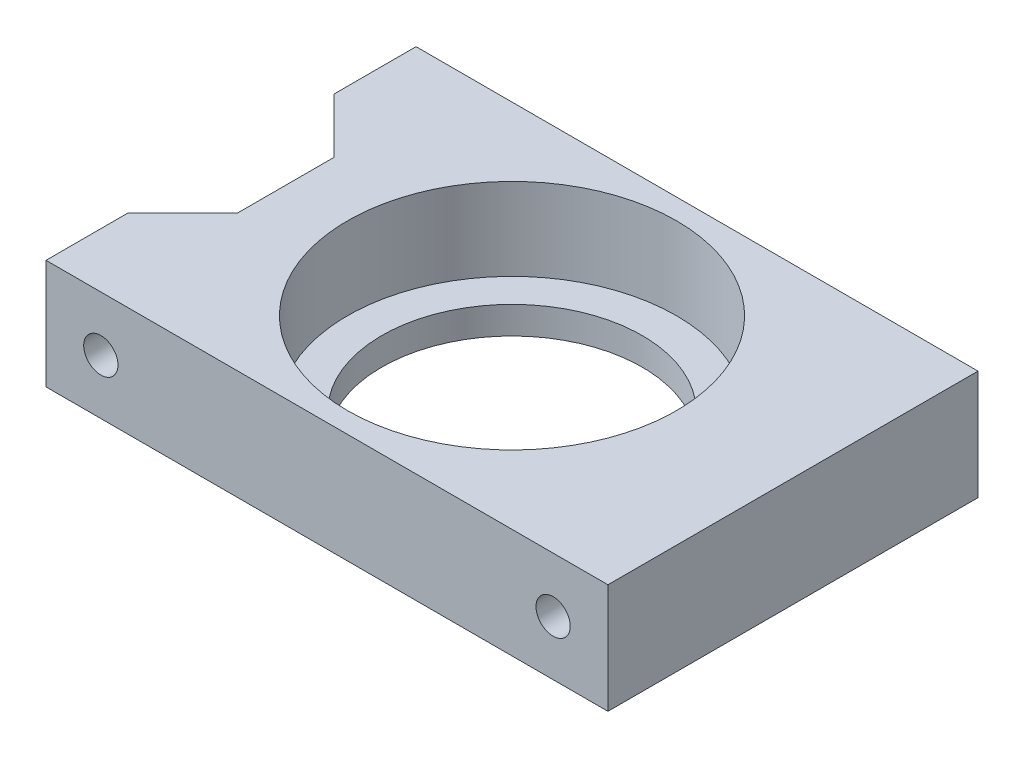
SolidWorks part; units mm, degrees
ref_plane "Спереди" through (0, 0, 0) normal (0, 0, 1) x (1, 0, 0)
ref_plane "Сверху" through (0, 0, 0) normal (0, 1, 0) x (1, 0, 0)
ref_plane "Справа" through (0, 0, 0) normal (1, 0, 0) x (0, 0, -1)
sketch "Эскиз1" plane through (0, 0, 0) normal (0, 1, 0) x (1, 0, 0)
  line L1 (-20.5, -13.5) -> (20.5, -13.5)
  line L2 (-20.5, -13.5) -> (-20.5, 13.5)
  line L3 (-20.5, 13.5) -> (20.5, 13.5)
  line L4 (20.5, -13.5) -> (20.5, 13.5)
  line L5 (-20.5, -13.5) -> (20.5, 13.5) construction
  line L6 (-20.5, 13.5) -> (20.5, -13.5) construction
  circle A0 centre (0, 0) radius 9.5
  point P0 (0, 0)
  dimension "D3" = 19
  dimension "D1" = 41
  dimension "D2" = 27
extrude "Бобышка-Вытянуть1" add sketch "Эскиз1" along normal blind 8
sketch "Эскиз2" plane through (0, 8, 0) normal (0, 1, 0) x (1, 0, 0)
  circle A0 centre (0, 0) radius 12
  dimension "D1" = 24
extrude "Вырез-Вытянуть1" cut sketch "Эскиз2" against normal blind 6
sketch "Эскиз3" plane through (0, 8, 0) normal (0, 1, 0) x (1, 0, 0)
  line L0 (-20.5, 7.5) -> (-16.5, 3.5)
  line L1 (-20.5, 13.5) -> (-20.5, -13.5) construction
  line L2 (-31.3013, 0) -> (32.4762, 0) construction
  line L3 (-20.5, -7.5) -> (-16.5, -3.5)
  line L4 (-16.5, 3.5) -> (-16.5, -3.5)
  line L5 (-20.5, 7.5) -> (-20.5, -7.5)
  dimension "D1" = 6
  dimension "D2" = 4
  dimension "D3" = 135
extrude "Вырез-Вытянуть2" cut sketch "Эскиз3" against normal blind 8
sketch "Эскиз4" plane through (0, 0, 13.5) normal (0, 0, 1) x (1, 0, 0)
  line L0 (-20.5, 0) -> (20.5, 0) construction
  line L1 (0, 17.4348) -> (0, -9.6659) construction
  circle A0 centre (-16.5, 4) radius 1.25
  circle A1 centre (16.5, 4) radius 1.25
  point P4 (0, 0)
  point P5 (0, 0)
  dimension "D1" = 2.5
  dimension "D2" = 4
  dimension "D3" = 16.5
extrude "Вырез-Вытянуть3" cut sketch "Эскиз4" against normal blind 7
sketch "Эскиз5" plane through (0, 0, -13.5) normal (0, 0, -1) x (-1, 0, 0)
  line L0 (0, 13.7764) -> (0, -13.5808) construction
  circle A0 centre (-16.5, 4) radius 1.25
  circle A1 centre (16.5, 4) radius 1.25
  dimension "D1" = 2.5
  dimension "D2" = 16.5
  dimension "D3" = 4
extrude "Вырез-Вытянуть4" cut sketch "Эскиз5" against normal blind 7
